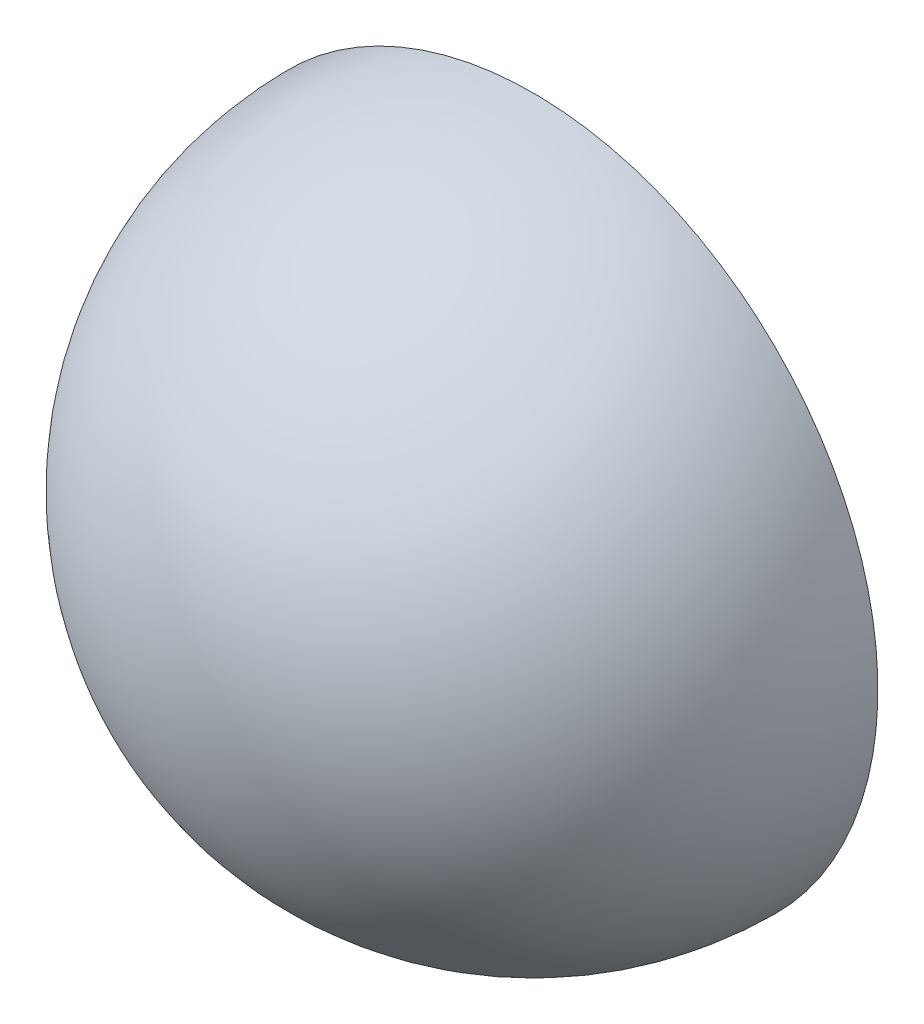
SolidWorks part; units mm, degrees
ref_plane "Front Plane" through (0, 0, 0) normal (0, 0, 1) x (1, 0, 0)
ref_plane "Top Plane" through (0, 0, 0) normal (0, 1, 0) x (1, 0, 0)
ref_plane "Right Plane" through (0, 0, 0) normal (1, 0, 0) x (0, 0, -1)
sketch "Sketch1" plane through (0, 0, 0) normal (0, 0, 1) x (1, 0, 0)
  line L0 (0, 5) -> (0, -5)
  arc A0 (0, -5) -> (0, 5) centre (0, 0) ccw
  dimension "D1" = 10
  dimension "D2" = 10
revolve "Revolve1" add sketch "Sketch1" angle 180 about L0
